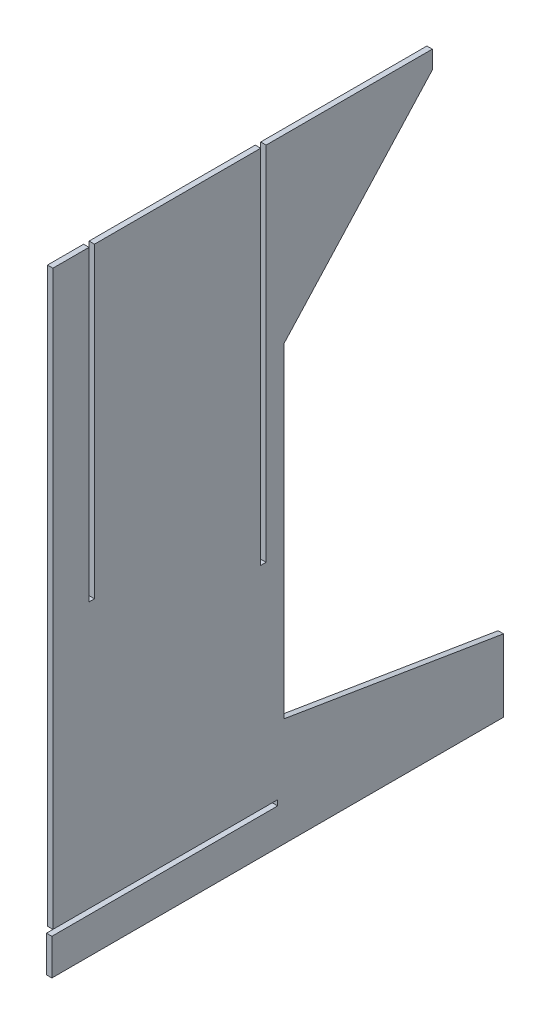
SolidWorks part; units mm, degrees
ref_plane "Front Plane" through (0, 0, 0) normal (0, 0, 1) x (1, 0, 0)
ref_plane "Top Plane" through (0, 0, 0) normal (0, 1, 0) x (1, 0, 0)
ref_plane "Right Plane" through (0, 0, 0) normal (1, 0, 0) x (0, 0, -1)
sketch "Sketch1" plane through (0, 0, 0) normal (1, 0, 0) x (0, 0, -1)
  line L2 (3.5697, -49.9035) -> (3.5697, -229.9035)
  line L3 (3.5697, -229.9035) -> (125, -249.9035)
  line L4 (125, -249.9035) -> (125, -289.9035)
  line L5 (125, -289.9035) -> (-125, -289.9035)
  line L6 (-125, -289.9035) -> (-125, -269.9035)
  line L7 (-125, -269.9035) -> (0, -269.9035)
  line L8 (0, -269.9035) -> (0, -266.9035)
  line L9 (0, -266.9035) -> (-124.4303, -266.9035)
  line L10 (-124.4303, -266.9035) -> (-124.4303, 50.096)
  line L11 (85.5697, 50.096) -> (-6.4303, 50.096)
  line L12 (-6.4303, 50.096) -> (-6.4303, -149.9035)
  line L13 (-6.4303, -149.9035) -> (-9.4303, -149.9035)
  line L14 (-9.4303, -149.9035) -> (-9.4303, 50.096)
  line L15 (-9.4303, 50.096) -> (-101.4303, 50.096)
  line L16 (-101.4303, 50.096) -> (-101.4303, -119.904)
  line L17 (-101.4303, -119.904) -> (-104.4303, -119.904)
  line L18 (-104.4303, -119.904) -> (-104.4303, 50.096)
  line L19 (-104.4303, 50.096) -> (-124.4303, 50.096)
  line L20 (85.5697, 50.096) -> (85.5697, 40.096)
  line L21 (85.5697, 40.096) -> (3.5697, -49.9035)
  dimension "D1" = 210
  dimension "D2" = 340
  dimension "D3" = 20
  dimension "D4" = 3
  dimension "D5" = 3
  dimension "D6" = 3
  dimension "D7" = 180
  dimension "D8" = 40
  dimension "D9" = 10
  dimension "D10" = 20
  dimension "D11" = 60
  dimension "D12" = 125
  dimension "D13" = 250
  dimension "D14" = 170
  dimension "D15" = 117
  dimension "D16" = 10
extrude "Boss-Extrude1" add sketch "Sketch1" along normal blind 3
